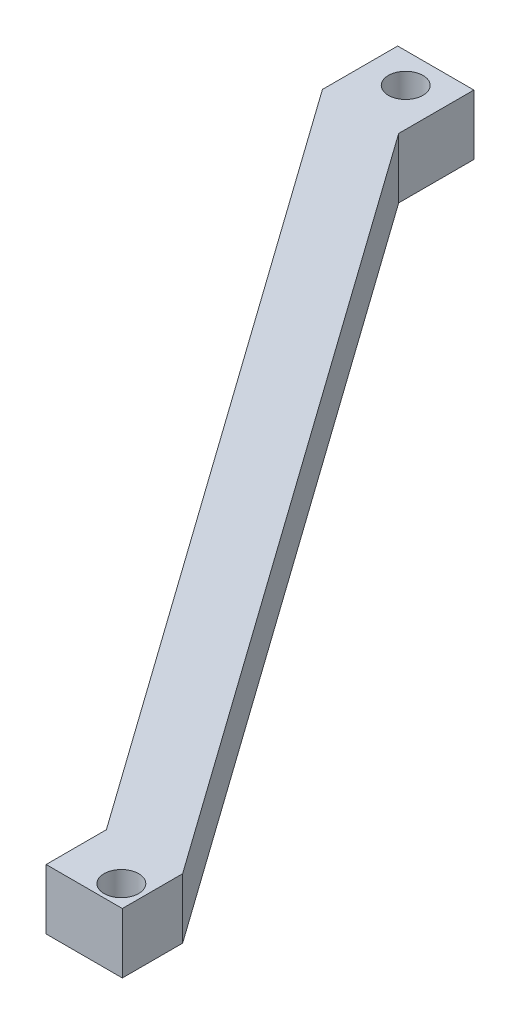
SolidWorks part; units mm, degrees
ref_plane "Front Plane" through (0, 0, 0) normal (0, 0, 1) x (1, 0, 0)
ref_plane "Top Plane" through (0, 0, 0) normal (0, 1, 0) x (1, 0, 0)
ref_plane "Right Plane" through (0, 0, 0) normal (1, 0, 0) x (0, 0, -1)
sketch "Sketch2" plane through (0, 0, 0) normal (0, 1, 0) x (1, 0, 0)
  line L0 (0, 0) -> (184.4011, -273.6718) construction
  line L1 (-12.6662, 10) -> (-12.6662, -15)
  line L2 (-12.6662, -15) -> (164.4781, -263.937)
  line L3 (164.4781, -263.937) -> (164.4781, -283.9672)
  line L4 (164.4781, -283.9672) -> (189.8104, -283.9672)
  line L5 (189.8104, -283.9672) -> (189.8104, -263.937)
  line L6 (189.8104, -263.937) -> (12.6662, -15)
  line L7 (12.6662, -15) -> (12.6662, 10)
  line L8 (12.6662, 10) -> (-12.6662, 10)
  point P5 (0, 10)
  dimension "D1" = 330
  dimension "D2" = 25
  dimension "D3" = 15
extrude "Boss-Extrude2" add sketch "Sketch2" along normal blind 20
sketch "Sketch3" plane through (0, 20, 0) normal (0, 1, 0) x (1, 0, 0)
  line L0 (164.4781, -283.9672) -> (189.8104, -283.9672) construction
  line L1 (164.4781, -263.937) -> (164.4781, -283.9672) construction
  circle A0 centre (0, 0) radius 5.75
  circle A1 centre (182.4781, -276.9672) radius 5.75
  dimension "D1" = 11.5
  dimension "D2" = 11.5
  dimension "D3" = 7
  dimension "D4" = 18
extrude "Cut-Extrude1" cut sketch "Sketch3" against normal through all
